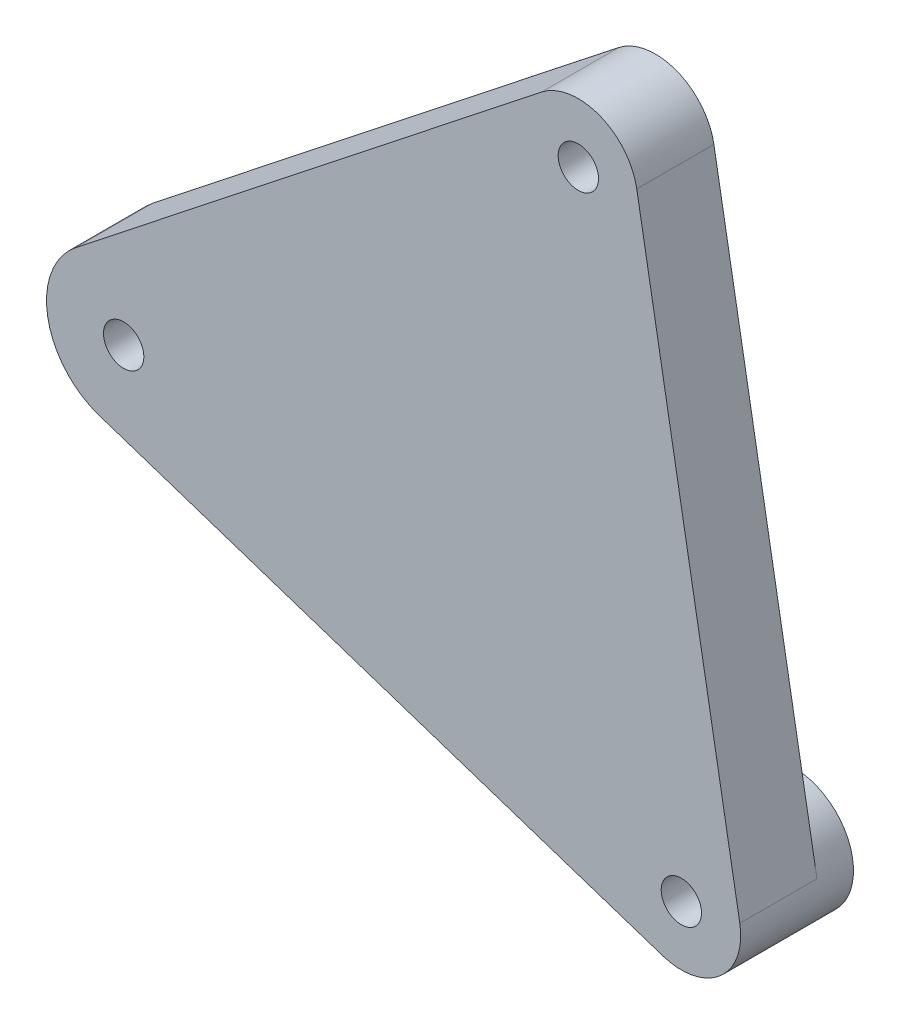
SolidWorks part; units mm, degrees
ref_plane "前视基准面" through (0, 0, 0) normal (0, 0, 1) x (1, 0, 0)
ref_plane "上视基准面" through (0, 0, 0) normal (0, 1, 0) x (1, 0, 0)
ref_plane "右视基准面" through (0, 0, 0) normal (1, 0, 0) x (0, 0, -1)
sketch "草图1" plane through (0, 0, 0) normal (0, 0, 1) x (1, 0, 0)
  line L0 (201.9846, -17.101) -> (155, 0) construction
  line L1 (155, 0) -> (193.3022, 32.1394) construction
  line L2 (193.3022, 32.1394) -> (201.9846, -17.101) construction
  line L3 (198.2263, 33.0076) -> (206.9087, -16.2328)
  line L4 (190.2046, 36.0643) -> (150.9731, 5.1024)
  line L5 (152.9611, -6.1719) -> (200.4163, -21.8487)
  circle A0 centre (201.9846, -17.101) radius 1.7
  circle A1 centre (155, 0) radius 1.7
  arc A2 (200.4163, -21.8487) -> (206.9087, -16.2328) centre (201.9846, -17.101) ccw
  arc A3 (150.9731, 5.1024) -> (152.9611, -6.1719) centre (155, 0) ccw
  circle A4 centre (193.3022, 32.1394) radius 1.7
  arc A5 (198.2263, 33.0076) -> (190.2046, 36.0643) centre (193.3022, 32.1394) ccw
  dimension "D1" = 13
  dimension "D2" = 10
  dimension "D3" = 50
  dimension "D4" = 50
extrude "凸台-拉伸1" add sketch "草图1" along normal blind 6.5 from offset 0.25
sketch "草图2" plane through (0, 0, 0.25) normal (0, 0, -1) x (-1, 0, 0)
  circle A0 centre (-201.9846, -17.101) radius 1.7 construction
  circle A1 centre (-201.9846, -17.101) radius 1.7
  circle A2 centre (-201.9846, -17.101) radius 5
extrude "凸台-拉伸2" add sketch "草图2" along normal blind 3
